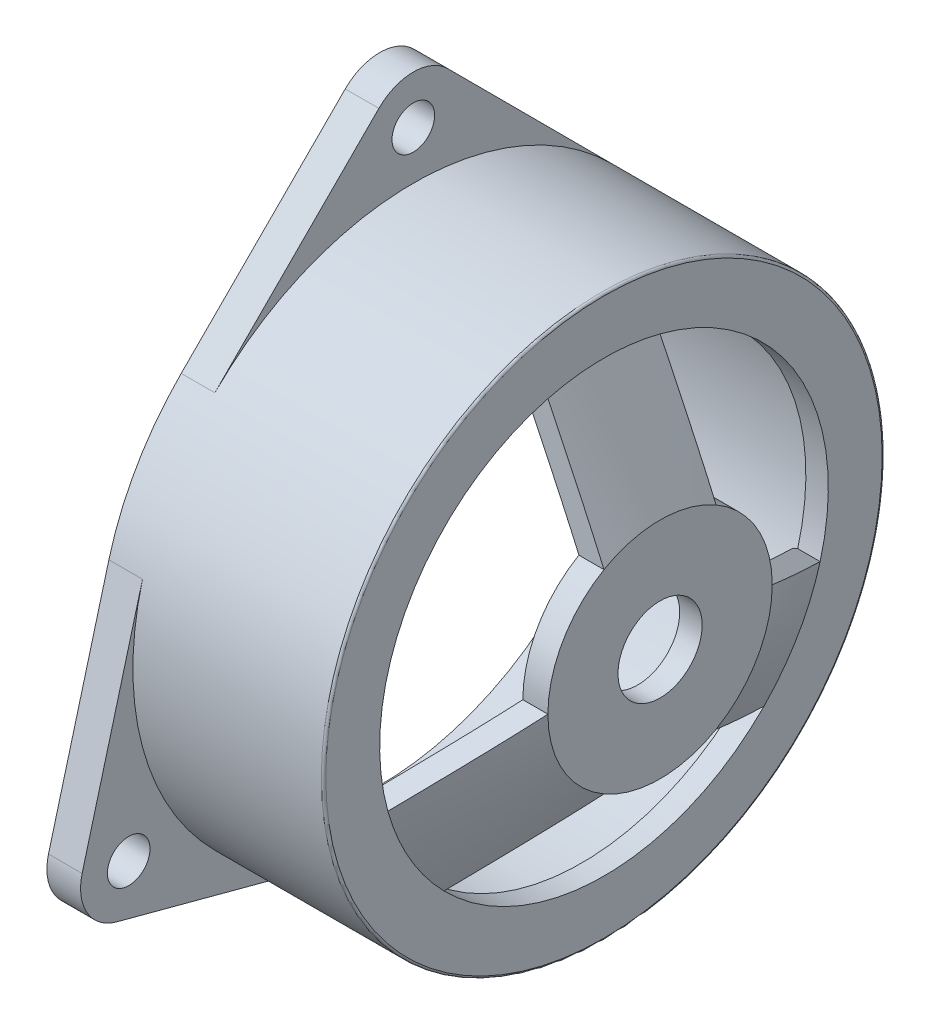
SolidWorks part; units mm, degrees
ref_plane "Front Plane" through (0, 0, 0) normal (0, 0, 1) x (1, 0, 0)
ref_plane "Top Plane" through (0, 0, 0) normal (0, 1, 0) x (1, 0, 0)
ref_plane "Right Plane" through (0, 0, 0) normal (1, 0, 0) x (0, 0, -1)
sketch "Sketch1" plane through (0, 0, 0) normal (1, 0, 0) x (0, 0, -1)
  circle A0 centre (0, 0) radius 50.8
  dimension "D1" = 101.6
ref_plane "Plane2" through (12.7, 0, 0) normal (1, 0, 0) x (0, 0, -1)
sketch "Sketch3" plane through (12.7, 0, 0) normal (1, 0, 0) x (0, 0, -1)
  circle A0 centre (0, 0) radius 25.4
loft "Loft1" add profiles "Sketch3", "Sketch1"
sketch "Sketch4" plane through (0, 0, 0) normal (-1, 0, 0) x (0, 0, 1)
  circle A0 centre (0, 0) radius 63.5
extrude "Boss-Extrude1" add sketch "Sketch4" along normal blind 50.8
shell "Shell1" thickness 5.08
sketch "Sketch5" plane through (12.7, 0, 0) normal (1, 0, 0) x (0, 0, -1)
  line L0 (0, -14.5059) -> (0, 73.1058) construction
  line L1 (-12.7, 21.997) -> (-12.7, 49.1869)
  line L2 (12.7, 21.997) -> (12.7, 49.1869)
  line L3 (-55.1416, 0) -> (54.5652, 0) construction
  line L4 (0, 0) -> (48.3641, -27.923) construction
  line L5 (48.9471, -13.5949) -> (25.4, 0)
  line L6 (12.7, -21.997) -> (36.2471, -35.592)
  line L7 (-51.222, -29.573) -> (0, 0) construction
  line L8 (-48.9471, -13.5949) -> (-25.4, 0)
  line L9 (-36.2471, -35.592) -> (-12.7, -21.997)
  circle A0 centre (0, 0) radius 25.4 construction
  circle A1 centre (0, 0) radius 50.8 construction
  arc A2 (-12.7, 49.1869) -> (-48.9471, -13.5949) centre (0, 0) ccw
  arc A3 (-36.2471, -35.592) -> (36.2471, -35.592) centre (0, 0) ccw
  arc A4 (48.9471, -13.5949) -> (12.7, 49.1869) centre (0, 0) ccw
  arc A5 (-25.4, 0) -> (-12.7, 21.997) centre (0, 0) cw
  arc A6 (12.7, 21.997) -> (25.4, 0) centre (0, 0) cw
  arc A7 (-12.7, -21.997) -> (12.7, -21.997) centre (0, 0) ccw
  dimension "D1" = 12.7
  dimension "D2" = 12.7
  dimension "D3" = 30
  dimension "D4" = 12.7
  dimension "D5" = 12.7
  dimension "D6" = 30
  dimension "D7" = 12.7
  dimension "D8" = 12.7
extrude "Cut-Extrude1" cut sketch "Sketch5" against normal blind 50.8
sketch "Sketch6" plane through (-50.8, 0, 0) normal (-1, 0, 0) x (0, 0, 1)
  line L0 (-7.7298, 82.1382) -> (-44.9408, 44.8618)
  line L1 (44.9408, 44.8618) -> (7.7952, 82.0727)
  arc A2 (-7.7298, 82.1382) -> (7.7952, 82.0727) centre (-0.0003, 74.2909) cw
  arc A7 (7.7624, 82.1055) -> (-7.7298, 82.1382) centre (0, 74.422) ccw
  circle A8 centre (0, 74.422) radius 4.826
  circle A10 centre (0, 0) radius 63.5 construction
  circle M6 centre (0, 0) radius 63.5
  dimension "D1" = 21.844
  dimension "D3" = 74.422
  dimension "D2" = 9.652
  dimension "D5" = 52.6706
  dimension "D4" = 52.578
extrude "Boss-Extrude3" add sketch "Sketch6" against normal blind 7.62 contours A2 L0 L1 A8 M6
fillet "Fillet1" radius 0.508 1 edges at (0, 0, 63.5)
sketch "Sketch7" plane through (12.7, 0, 0) normal (1, 0, 0) x (0, 0, -1)
  circle A0 centre (0, 0) radius 9.525
extrude "Cut-Extrude2" cut sketch "Sketch7" against normal through all
sketch "Sketch8" plane through (-50.8, 0, 0) normal (-1, 0, 0) x (0, 0, 1)
  circle A0 centre (0, 0) radius 58.42
  dimension "D1" = 116.84
sketch "Sketch9" plane through (-50.8, 0, 0) normal (-1, 0, 0) x (0, 0, 1)
  circle A0 centre (0, 0) radius 58.42
pattern_circular "CirPattern2" count 3 over 360 about axis through (0, 0, 0) along (1, 0, 0) of "Boss-Extrude3"
